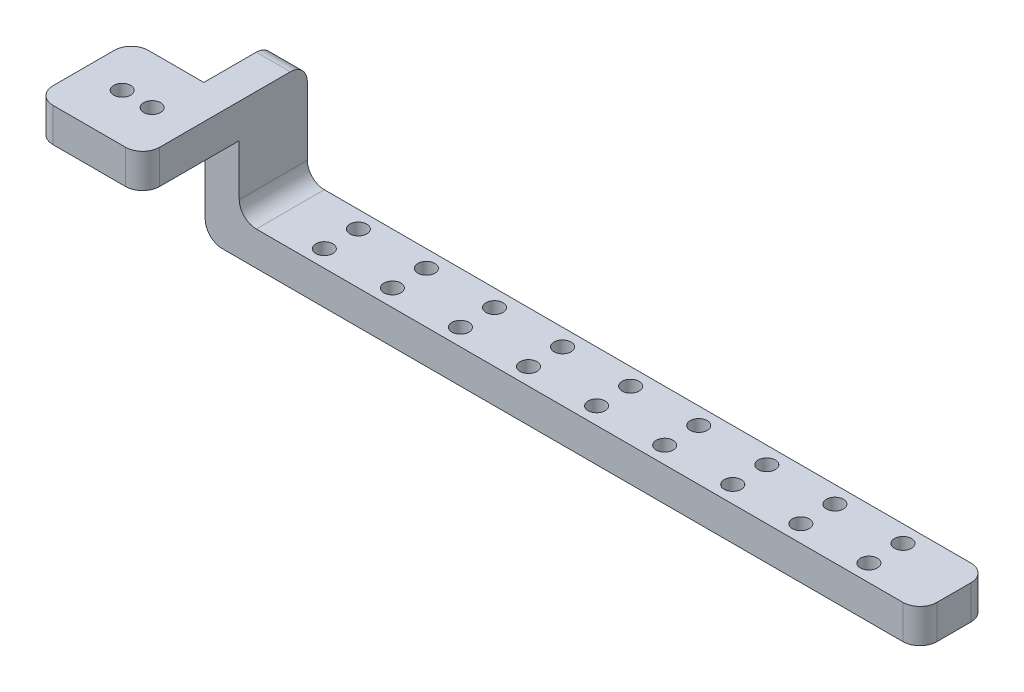
SolidWorks part; units mm, degrees
ref_plane "Front Plane" through (0, 0, 0) normal (0, 0, 1) x (1, 0, 0)
ref_plane "Top Plane" through (0, 0, 0) normal (0, 1, 0) x (1, 0, 0)
ref_plane "Right Plane" through (0, 0, 0) normal (1, 0, 0) x (0, 0, -1)
sketch "Sketch1" plane through (0, 0, 0) normal (0, 1, 0) x (1, 0, 0)
  line L1 (-20.7391, -8.89) -> (20.7391, -8.89)
  line L2 (-20.7391, -8.89) -> (-20.7391, 8.89)
  line L3 (-20.7391, 8.89) -> (20.7391, 8.89)
  line L4 (20.7391, -8.89) -> (20.7391, 8.89)
  line L5 (-20.7391, -8.89) -> (20.7391, 8.89) construction
  line L6 (-20.7391, 8.89) -> (20.7391, -8.89) construction
  line L7 (-8.0391, 0) -> (8.0391, 0) construction
  circle A0 centre (-8.0391, 0) radius 4.445
  circle A1 centre (13.6271, 0) radius 1.5875
  circle A2 centre (8.0391, 0) radius 1.5875
  point P0 (0, 0)
  point P6 (0, 0)
  dimension "D1" = 8.89
  dimension "D4" = 3.175
  dimension "D2" = 16.0782
  dimension "D3" = 5.588
  dimension "D5" = 17.78
  dimension "D6" = 12.7
extrude "Boss-Extrude1" add sketch "Sketch1" along normal blind 6.35
sketch "Sketch2" plane through (0, 0, -8.89) normal (0, 0, -1) x (-1, 0, 0)
  line L0 (-20.7391, 6.35) -> (20.7391, 6.35) construction
  line L1 (-20.7391, 0) -> (-14.3891, 0)
  line L2 (-20.7391, 0) -> (-20.7391, 6.35)
  line L3 (-20.7391, 6.35) -> (-14.3891, 6.35)
  line L4 (-14.3891, 0) -> (-14.3891, 6.35)
  dimension "D1" = 6.35
extrude "Boss-Extrude2" add sketch "Sketch2" along normal blind 0.254
sketch "Sketch3" plane through (0, 0, -9.144) normal (0, 0, -1) x (-1, 0, 0)
  line L1 (-14.3891, 6.35) -> (-20.7391, 6.35)
  line L2 (-14.3891, 6.35) -> (-14.3891, -19.05)
  line L3 (-14.3891, -19.05) -> (-20.7391, -19.05)
  line L4 (-20.7391, 6.35) -> (-20.7391, -19.05)
  dimension "D1" = 25.4
extrude "Boss-Extrude3" add sketch "Sketch3" along normal blind 12.7
sketch "Sketch4" plane through (20.7391, 0, 0) normal (1, 0, 0) x (0, 0, -1)
  line L0 (21.844, 6.35) -> (21.844, -19.05) construction
  line L1 (9.144, -19.05) -> (21.844, -19.05)
  line L2 (9.144, -19.05) -> (9.144, -12.7)
  line L3 (9.144, -12.7) -> (21.844, -12.7)
  line L4 (21.844, -19.05) -> (21.844, -12.7)
  dimension "D1" = 6.35
extrude "Boss-Extrude4" add sketch "Sketch4" along normal blind 127
sketch "Sketch5" plane through (0, -12.7, 0) normal (0, 1, 0) x (1, 0, 0)
  line L0 (20.7391, 15.494) -> (147.7391, 15.494) construction
  line L1 (20.7391, 21.844) -> (20.7391, 9.144) construction
  line L2 (147.7391, 21.844) -> (147.7391, 9.144) construction
  line L3 (33.4391, 12.319) -> (33.4391, 18.669) construction
  line L4 (46.1391, 12.319) -> (46.1391, 18.669) construction
  line L5 (58.8391, 12.319) -> (58.8391, 18.669) construction
  line L6 (71.5391, 12.319) -> (71.5391, 18.669) construction
  line L7 (84.2391, 12.319) -> (84.2391, 18.669) construction
  line L8 (96.9391, 12.319) -> (96.9391, 18.669) construction
  line L9 (109.6391, 12.319) -> (109.6391, 18.669) construction
  line L10 (122.3391, 12.319) -> (122.3391, 18.669) construction
  line L11 (135.0391, 12.319) -> (135.0391, 18.669) construction
  line L12 (33.4391, 12.319) -> (46.1391, 12.319) construction
  circle A0 centre (33.4391, 18.669) radius 1.5875
  circle A1 centre (33.4391, 12.319) radius 1.5875
  circle A2 centre (46.1391, 12.319) radius 1.5875
  circle A3 centre (46.1391, 18.669) radius 1.5875
  circle A4 centre (58.8391, 12.319) radius 1.5875
  circle A5 centre (58.8391, 18.669) radius 1.5875
  circle A6 centre (71.5391, 12.319) radius 1.5875
  circle A7 centre (71.5391, 18.669) radius 1.5875
  circle A8 centre (84.2391, 12.319) radius 1.5875
  circle A9 centre (84.2391, 18.669) radius 1.5875
  circle A10 centre (96.9391, 12.319) radius 1.5875
  circle A11 centre (96.9391, 18.669) radius 1.5875
  circle A12 centre (109.6391, 12.319) radius 1.5875
  circle A13 centre (109.6391, 18.669) radius 1.5875
  circle A14 centre (122.3391, 12.319) radius 1.5875
  circle A15 centre (122.3391, 18.669) radius 1.5875
  circle A16 centre (135.0391, 12.319) radius 1.5875
  circle A17 centre (135.0391, 18.669) radius 1.5875
  point P9 (33.4391, 15.494)
  dimension "D2" = 3.175
  dimension "D1" = 12.7
  dimension "D3" = 6.35
  dimension "D5" = 12.7
  dimension "D4" = 9
extrude "Cut-Extrude1" cut sketch "Sketch5" against normal through all
sketch "Sketch6" plane through (0, 6.35, 0) normal (0, 1, 0) x (1, 0, 0)
  line L0 (-20.7391, -8.89) -> (20.7391, -8.89) construction
  line L1 (-20.7391, 8.89) -> (0.8509, 8.89)
  line L2 (-20.7391, 8.89) -> (-20.7391, -8.89)
  line L3 (-20.7391, -8.89) -> (0.8509, -8.89)
  line L4 (0.8509, 8.89) -> (0.8509, -8.89)
  dimension "D1" = 21.59
extrude "Cut-Extrude2" cut sketch "Sketch6" against normal through all
fillet "Fillet1" radius 3.175 8 edges at (14.3891, -19.05, -15.494) (147.7391, -15.875, -21.844) (147.7391, -15.875, -9.144) (0.8509, 3.175, 8.89) (0.8509, 3.175, -8.89) (17.5641, 6.35, -21.844) (20.7391, -12.7, -15.494) (20.7391, 3.175, 8.89)
